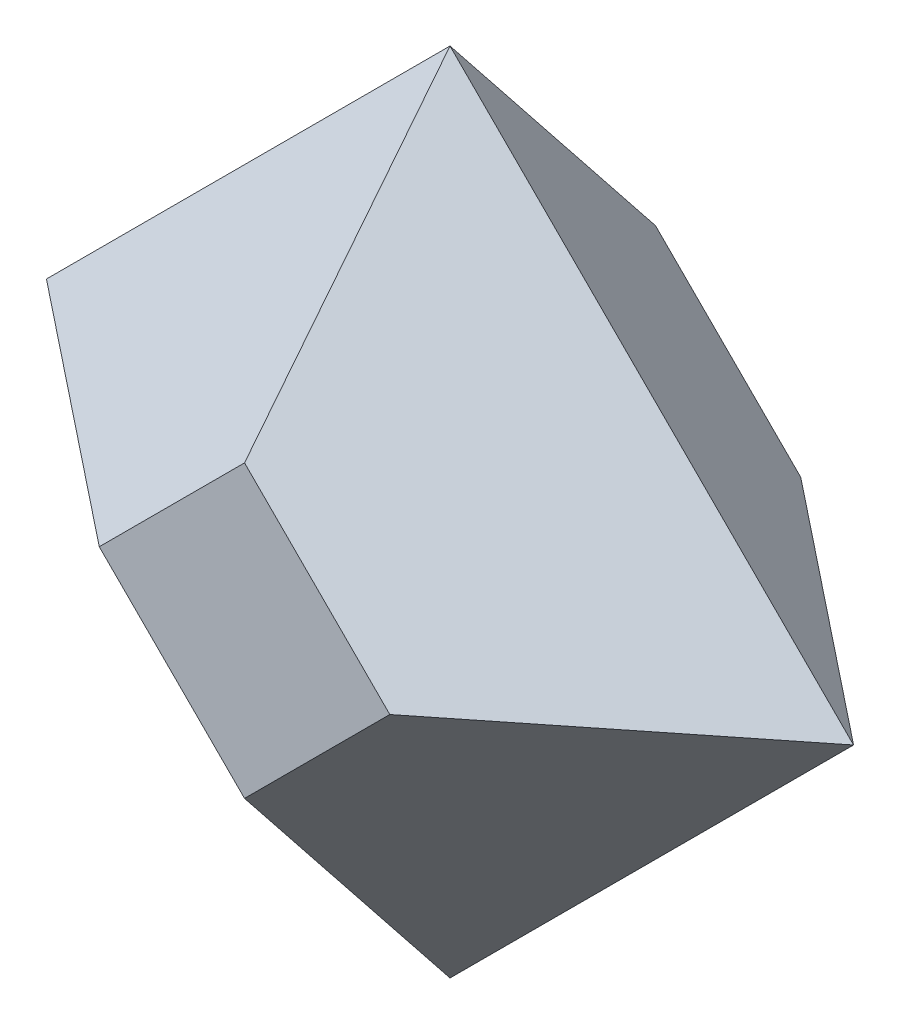
SolidWorks part; units mm, degrees
ref_plane "Alzado" through (0, 0, 0) normal (0, 0, 1) x (1, 0, 0)
ref_plane "Planta" through (0, 0, 0) normal (0, 1, 0) x (1, 0, 0)
ref_plane "Vista lateral" through (0, 0, 0) normal (1, 0, 0) x (0, 0, -1)
sketch "Croquis1" plane through (0, 0, 0) normal (0, 0, 1) x (1, 0, 0)
  line L1 (0, 17.6777) -> (-17.6777, 0)
  line L2 (-17.6777, 0) -> (0, -17.6777)
  line L3 (0, -17.6777) -> (17.6777, 0)
  line L4 (17.6777, 0) -> (0, 17.6777)
  circle A0 centre (0, 0) radius 12.5 construction
  dimension "D1" = 25
ref_plane "Plano1" through (0, 0, 9) normal (0, 0, 1) x (1, 0, 0)
sketch "Croquis2" plane through (0, 0, 9) normal (0, 0, 1) x (1, 0, 0)
  line L1 (0, 6.364) -> (-6.364, 0)
  line L2 (-6.364, 0) -> (0, -6.364)
  line L3 (0, -6.364) -> (6.364, 0)
  line L4 (6.364, 0) -> (0, 6.364)
  circle A0 centre (0, 0) radius 4.5 construction
  dimension "D1" = 9
loft "Recubrir1" add profiles "Croquis1", "Croquis2"
ref_plane "Plano2" through (0, 0, -9) normal (0, 0, -1) x (-1, 0, 0)
sketch "Croquis4" plane through (0, 0, -9) normal (0, 0, -1) x (-1, 0, 0)
  line L1 (0, -6.364) -> (6.364, 0)
  line L2 (6.364, 0) -> (0, 6.364)
  line L3 (0, 6.364) -> (-6.364, 0)
  line L4 (-6.364, 0) -> (0, -6.364)
  circle A0 centre (0, 0) radius 4.5 construction
  dimension "D1" = 9
sketch "Croquis5" plane through (0, 0, 0) normal (0, 0, -1) x (-1, 0, 0)
  line L1 (0, 17.6777) -> (-17.6777, 0)
  line L2 (-17.6777, 0) -> (0, -17.6777)
  line L3 (0, -17.6777) -> (17.6777, 0)
  line L4 (17.6777, 0) -> (0, 17.6777)
  circle A0 centre (0, 0) radius 12.5 construction
  dimension "D1" = 25
loft "Recubrir2" add profiles "Croquis5", "Croquis4"
